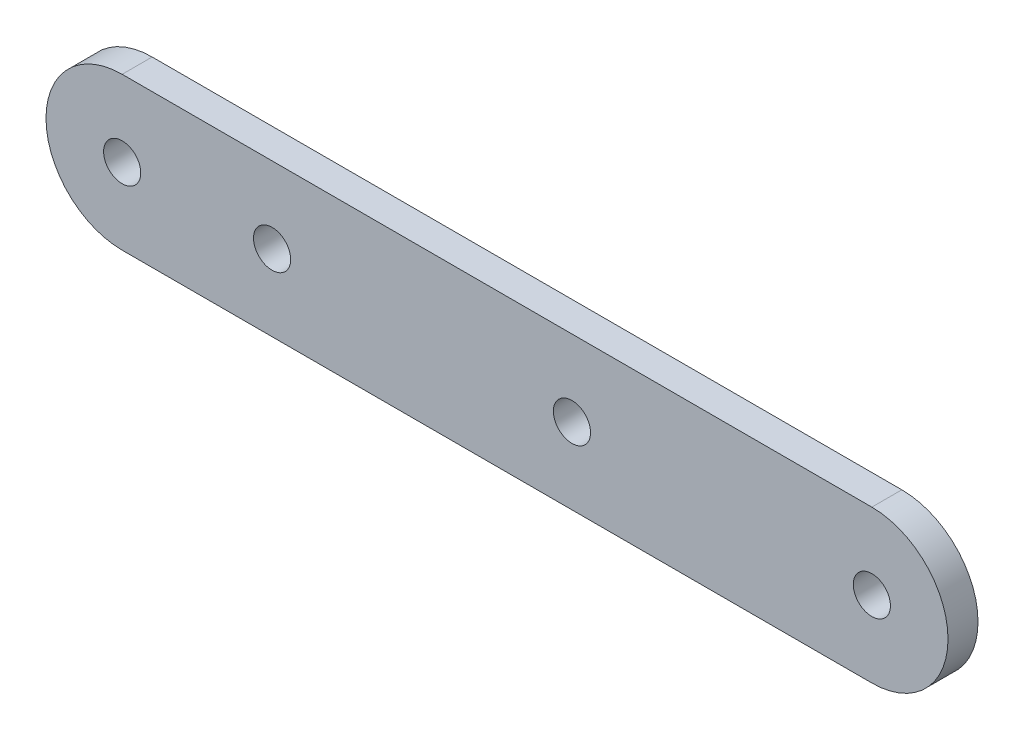
SolidWorks part; units mm, degrees
material "Ceramic Porcelain"
ref_plane "Front Plane" through (0, 0, 0) normal (0, 0, 1) x (1, 0, 0)
ref_plane "Top Plane" through (0, 0, 0) normal (0, 1, 0) x (1, 0, 0)
ref_plane "Right Plane" through (0, 0, 0) normal (1, 0, 0) x (0, 0, -1)
sketch "Sketch1" plane through (0, 0, 0) normal (0, 0, 1) x (1, 0, 0)
  line L1 (0, -12.7) -> (125, -12.7)
  line L3 (0, 12.7) -> (125, 12.7)
  circle A0 centre (0, 0) radius 3.1
  arc A1 (0, 12.7) -> (0, -12.7) centre (0, 0) ccw
  circle A2 centre (125, 0) radius 3.1
  arc A3 (125, 12.7) -> (125, -12.7) centre (125, 0) cw
  circle A4 centre (25, 0) radius 3.1
  circle A5 centre (75, 0) radius 3.1
  dimension "D4" = 6.2
  dimension "D2" = 25.4
  dimension "D3" = 125
  dimension "D5" = 50
  dimension "D6" = 25
extrude "Boss-Extrude1" add sketch "Sketch1" along normal blind 5
